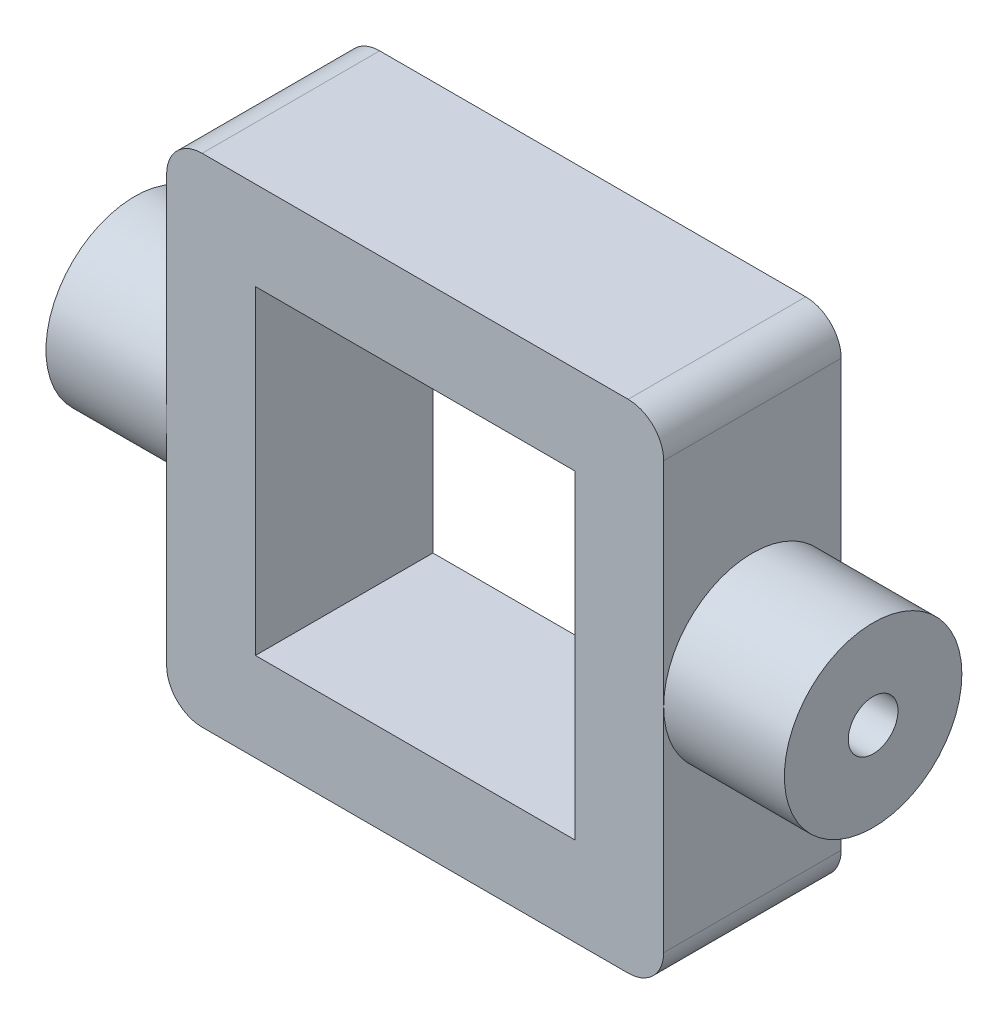
SolidWorks part; units mm, degrees
material "Sculpteo SLS"
ref_plane "Front Plane" through (0, 0, 0) normal (0, 0, 1) x (1, 0, 0)
ref_plane "Top Plane" through (0, 0, 0) normal (0, 1, 0) x (1, 0, 0)
ref_plane "Right Plane" through (0, 0, 0) normal (1, 0, 0) x (0, 0, -1)
sketch "Sketch1" plane through (0, 0, 0) normal (0, 0, 1) x (1, 0, 0)
  line L1 (7, -7) -> (-7, -7)
  line L2 (7, -7) -> (7, 7)
  line L3 (7, 7) -> (-7, 7)
  line L4 (-7, -7) -> (-7, 7)
  line L5 (7, -7) -> (-7, 7) construction
  line L6 (7, 7) -> (-7, -7) construction
  line L7 (4.5, -4.5) -> (-4.5, -4.5)
  line L8 (4.5, -4.5) -> (4.5, 4.5)
  line L9 (4.5, 4.5) -> (-4.5, 4.5)
  line L10 (-4.5, -4.5) -> (-4.5, 4.5)
  line L11 (4.5, -4.5) -> (-4.5, 4.5) construction
  line L12 (4.5, 4.5) -> (-4.5, -4.5) construction
  point P0 (0, 0)
  point P6 (0, 0)
  dimension "D1" = 14
  dimension "D2" = 14
  dimension "D3" = 9
  dimension "D4" = 9
extrude "Boss-Extrude1" add sketch "Sketch1" along normal mid plane 5
sketch "Sketch3" plane through (7, 0, 0) normal (1, 0, 0) x (0, 0, -1)
  circle A0 centre (0, 0) radius 2.5
  dimension "D1" = 5
extrude "Boss-Extrude2" add sketch "Sketch3" along normal blind 3.4
sketch "Sketch4" plane through (10.4, 0, 0) normal (1, 0, 0) x (0, 0, -1)
  circle A0 centre (0, 0) radius 0.7
  dimension "D1" = 1.4
extrude "Cut-Extrude1" cut sketch "Sketch4" against normal blind 5
mirror "Mirror1" about plane through (0, 0, 0) normal (1, 0, 0) of "Cut-Extrude1", "Boss-Extrude2"
fillet "Fillet1" radius 1 4 edges at (-7, 7, 0) (-7, -7, 0) (7, -7, 0) (7, 7, 0)
